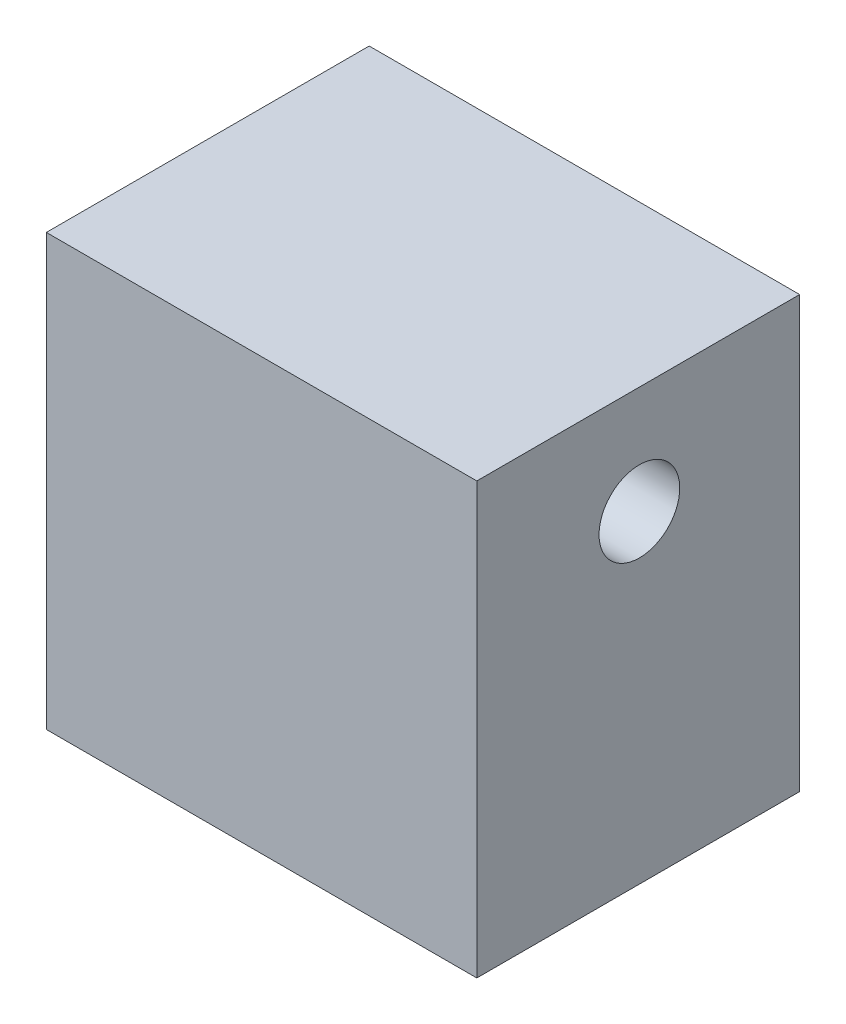
SolidWorks part; units mm, degrees
ref_plane "Front Plane" through (0, 0, 0) normal (0, 0, 1) x (1, 0, 0)
ref_plane "Top Plane" through (0, 0, 0) normal (0, 1, 0) x (1, 0, 0)
ref_plane "Right Plane" through (0, 0, 0) normal (1, 0, 0) x (0, 0, -1)
sketch "Sketch1" plane through (0, 0, 0) normal (0, 0, 1) x (1, 0, 0)
  line L1 (25.4, 25.4) -> (-25.4, 25.4)
  line L2 (25.4, 25.4) -> (25.4, -25.4)
  line L3 (25.4, -25.4) -> (-25.4, -25.4)
  line L4 (-25.4, 25.4) -> (-25.4, -25.4)
  line L5 (25.4, 25.4) -> (-25.4, -25.4) construction
  line L6 (25.4, -25.4) -> (-25.4, 25.4) construction
  point P0 (0, 0)
  dimension "D1" = 50.8
  dimension "D2" = 50.8
extrude "Boss-Extrude1" add sketch "Sketch1" along normal blind 38.1
sketch "Sketch3" plane through (0, -25.4, 0) normal (0, -1, 0) x (1, 0, 0)
  line L1 (25.4, 38.1) -> (25.4, 0) construction
  circle A0 centre (0, 19.05) radius 5.588
  point P5 (25.4, 19.05)
  dimension "D1" = 11.176
extrude "Cut-Extrude1" cut sketch "Sketch3" against normal blind 25.4
sketch "Sketch4" plane through (-25.4, 0, 0) normal (-1, 0, 0) x (0, 0, 1)
  line L0 (38.1, -25.4) -> (0, -25.4) construction
  circle A0 centre (18.915, 12.7) radius 4.7625
  dimension "D1" = 9.525
  dimension "D2" = 38.1
extrude "Cut-Extrude2" cut sketch "Sketch4" against normal through all
